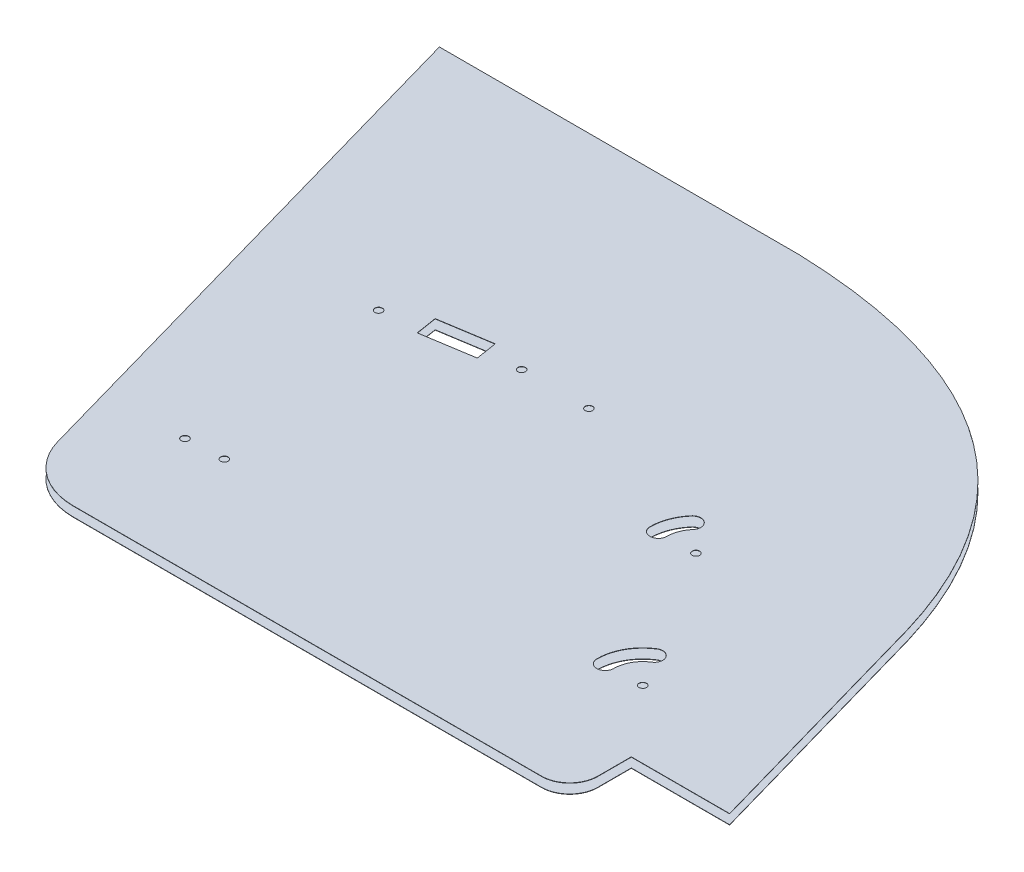
SolidWorks part; units mm, degrees
material "Thornel Mat VMA"
ref_plane "Płaszczyzna XY" through (0, 0, 0) normal (0, 0, 1) x (1, 0, 0)
ref_plane "Płaszczyzna XZ" through (0, 0, 0) normal (0, 1, 0) x (1, 0, 0)
ref_plane "Płaszczyzna YZ" through (0, 0, 0) normal (1, 0, 0) x (0, 0, -1)
sketch "Szkic1" plane through (0, 445, 0) normal (0, -1, 0) x (1, 0, 0)
  line L6 (-783.4364, -69.1493) -> (-400.0381, -69.1493)
  line L7 (4.1571, 219.2388) -> (79.2234, 484.0542)
  line L8 (79.2234, 484.0542) -> (-25.5904, 484.0542)
  line L9 (-25.5904, 484.0542) -> (-25.5904, 519.756)
  line L10 (-55.5904, 549.756) -> (-555.0819, 549.756)
  line L11 (-622.4285, 498.8465) -> (-783.4364, -69.1493)
  line L12 (-783.4364, -69.1493) -> (-400.0381, -69.1493)
  line L13 (4.1571, 219.2388) -> (79.2234, 484.0542)
  line L14 (79.2234, 484.0542) -> (-25.5904, 484.0542)
  line L15 (-25.5904, 484.0542) -> (-25.5904, 519.756)
  line L16 (-55.5904, 549.756) -> (-555.0819, 549.756)
  line L17 (-622.4285, 498.8465) -> (-783.4364, -69.1493)
  arc A2 (-25.5904, 519.756) -> (-55.5904, 549.756) centre (-55.5904, 519.756) ccw
  arc A3 (-555.0819, 549.756) -> (-622.4285, 498.8465) centre (-555.0819, 479.756) ccw
  arc A4 (-25.5904, 519.756) -> (-55.5904, 549.756) centre (-55.5904, 519.756) ccw
  arc A5 (-555.0819, 549.756) -> (-622.4285, 498.8465) centre (-555.0819, 479.756) ccw
  parabola Q1 (-400.0381, -69.1493) -> (4.1571, 219.2388) focus (-223.0428, 157.9749) apex (-110.088, 30.7152)
  parabola Q2 (-400.0381, -69.1493) -> (4.1571, 219.2388) focus (-223.0428, 157.9749) apex (-110.088, 30.7152)
  dimension "D1" = 0
extrude "Dodanie-wyciągnięcie1" add sketch "Szkic1" along normal blind 0.3
ref_plane "Płaszczyzna1" through (0, 450, 0) normal (0, 1, 0) x (1, 0, 0)
mirror "Lustro2" about plane through (0, 450, 0) normal (0, 1, 0) of bodies 102
sketch "Szkic3" plane through (0, 444.7, 0) normal (0, -1, 0) x (1, 0, 0)
  line L0 (-524.3207, 205.6019) -> (-482.8377, 199.0316)
  line L1 (-482.8377, 199.0316) -> (-486.4357, 176.3148)
  line L2 (-486.4357, 176.3148) -> (-527.9187, 182.8851)
  line L3 (-527.9187, 182.8851) -> (-524.3207, 205.6019)
  circle A0 centre (-572.688, 206.3657) radius 4
  circle A1 centre (-441.6637, 184.9064) radius 4
  circle A2 centre (-369.9079, 184.9064) radius 4
  circle A3 centre (-557.5005, 428.0763) radius 4
  circle A4 centre (-517.5005, 426.0793) radius 4
  circle A6 centre (-179.1662, 261.5446) radius 4
  circle A8 centre (-85.5135, 411.9205) radius 4
  arc A24 (-116.5135, 411.9205) -> (-102.1201, 385.7438) centre (-85.5135, 411.9205) ccw
  arc A25 (-134.5135, 411.9205) -> (-111.7627, 370.5444) centre (-85.5135, 411.9205) ccw
  arc A26 (-111.7627, 370.5444) -> (-102.1201, 385.7438) centre (-106.9414, 378.1441) ccw
  arc A27 (-116.5135, 411.9205) -> (-134.5135, 411.9205) centre (-125.5135, 411.9205) ccw
  arc A30 (-210.1662, 261.5446) -> (-202.5154, 241.153) centre (-179.1662, 261.5446) ccw
  arc A31 (-228.1662, 261.5446) -> (-216.073, 229.3127) centre (-179.1662, 261.5446) ccw
  arc A32 (-216.073, 229.3127) -> (-202.5154, 241.153) centre (-209.2942, 235.2328) ccw
  arc A33 (-210.1662, 261.5446) -> (-228.1662, 261.5446) centre (-219.1662, 261.5446) ccw
  dimension "D1" = 62
  dimension "D2" = 98
  dimension "D3" = 62
  dimension "D4" = 98
extrude "Wytnij-wyciągnięcie1" cut sketch "Szkic3" against normal blind 40
sketch "Szkic4" plane through (0, 455.3, 0) normal (0, 1, 0) x (1, 0, 0)
  line L0 (-527.9187, -182.8851) -> (-486.4357, -176.3148)
  line L1 (-486.4357, -176.3148) -> (-479.5219, -175.2198)
  line L2 (-527.9187, -182.8851) -> (-534.8325, -183.9801)
  line L3 (-479.5219, -175.2198) -> (-475.9239, -197.9366)
  line L4 (-482.8377, -199.0316) -> (-475.9239, -197.9366)
  line L5 (-482.8377, -199.0316) -> (-531.2345, -206.6969)
  line L6 (-534.8325, -183.9801) -> (-531.2345, -206.6969)
  dimension "D1" = 7
  dimension "D2" = 7
extrude "Wytnij-wyciągnięcie2" cut sketch "Szkic4" against normal through all
